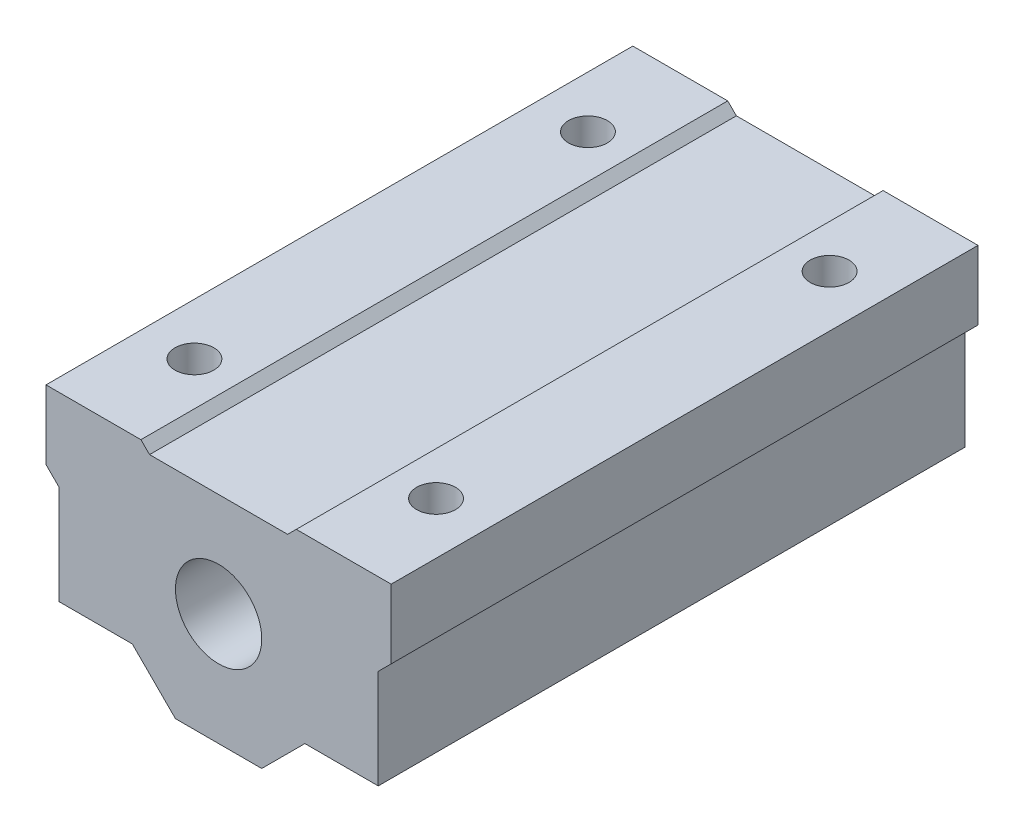
SolidWorks part; units mm, degrees
ref_plane "前视基准面" through (0, 0, 0) normal (0, 0, 1) x (1, 0, 0)
ref_plane "上视基准面" through (0, 0, 0) normal (0, 1, 0) x (1, 0, 0)
ref_plane "右视基准面" through (0, 0, 0) normal (1, 0, 0) x (0, 0, -1)
sketch "Sketch1" plane through (0, 0, 0) normal (0, 0, 1) x (1, 0, 0)
  line L0 (0, 12) -> (0, -13) construction
  line L1 (-18.5, -8) -> (-10, -8)
  line L2 (-20, 5) -> (-20, 13)
  line L3 (-20, 13) -> (-9, 13)
  line L7 (-9, 13) -> (-8, 12)
  line L8 (-8, 12) -> (8, 12)
  line L9 (-20, 5) -> (-18.5, 3.5)
  line L10 (-18.5, 3.5) -> (-18.5, -8)
  line L11 (-10, -8) -> (-5, -13)
  line L12 (-5, -13) -> (5, -13)
  line L13 (10, -8) -> (5, -13)
  line L14 (9, 13) -> (8, 12)
  line L18 (10, -8) -> (18.5, -8)
  line L20 (18.5, 3.5) -> (18.5, -8)
  line L21 (20, 5) -> (18.5, 3.5)
  line L22 (20, 5) -> (20, 13)
  line L23 (20, 13) -> (9, 13)
  circle A1 centre (0, 0) radius 5
  point P0 (0, 0)
  point P2 (18.5, 4.2929)
  point P21 (0, -13)
  point P23 (0, 12)
  point P25 (0, 0)
  point P27 (20, 0.3339)
  point P28 (0, 0)
  point P29 (0, -13)
  point P30 (0, 12)
  point P31 (0, 0)
  point P32 (9.301, 13)
  dimension "D1" = 10
  dimension "D2" = 8
  dimension "D3" = 13
  dimension "D4" = 20
  dimension "D5" = 26
  dimension "D6" = 21
  dimension "D7" = 1.5
  dimension "D8" = 45
  dimension "D9" = 1
  dimension "D10" = 135
  dimension "D11" = 16
  dimension "D12" = 45
  dimension "D13" = 10
extrude "Extrude1" add sketch "Sketch1" along normal blind 68
sketch "Sketch2" plane through (0, 13, 0) normal (0, 1, 0) x (1, 0, 0)
  line L0 (0, 0) -> (0, -68) construction
  line L1 (-14, -56.8) -> (14, -56.8) construction
  line L2 (-14, -56.8) -> (-14, -11.2) construction
  line L3 (-14, -11.2) -> (14, -11.2) construction
  line L4 (14, -56.8) -> (14, -11.2) construction
  line L5 (-14, -56.8) -> (14, -11.2) construction
  line L6 (-14, -11.2) -> (14, -56.8) construction
  line L7 (8, -68) -> (-8, -68) construction
  line L8 (-20, -34) -> (20, -34) construction
  line L9 (-20, -68) -> (-20, 0) construction
  line L10 (20, -68) -> (20, 0) construction
  circle A0 centre (-14, -11.2) radius 2.25
  circle A1 centre (14, -11.2) radius 2.25
  circle A2 centre (14, -56.8) radius 2.25
  circle A3 centre (-14, -56.8) radius 2.25
  point P0 (0, -34)
  dimension "D3" = 4.5
  dimension "D1" = 45.6
  dimension "D2" = 28
extrude "Extrude2" cut sketch "Sketch2" against normal blind 68
